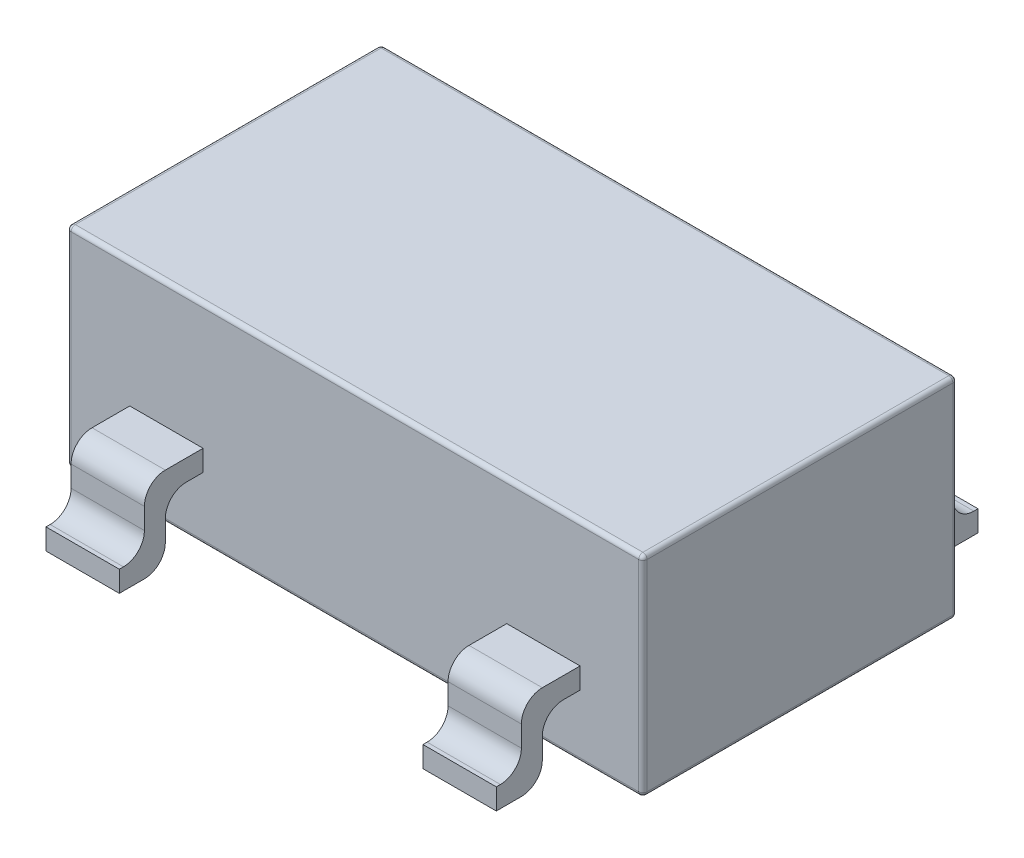
SolidWorks part; units mm, degrees
ref_plane "Front Plane" through (0, 0, 0) normal (0, 0, 1) x (1, 0, 0)
ref_plane "Top Plane" through (0, 0, 0) normal (0, 1, 0) x (1, 0, 0)
ref_plane "Right Plane" through (0, 0, 0) normal (1, 0, 0) x (0, 0, -1)
sketch "Sketch1" plane through (0, 0, 0) normal (0, 1, 0) x (1, 0, 0)
  line L1 (-1.375, -0.75) -> (1.375, -0.75)
  line L2 (-1.375, -0.75) -> (-1.375, 0.75)
  line L3 (-1.375, 0.75) -> (1.375, 0.75)
  line L4 (1.375, -0.75) -> (1.375, 0.75)
  line L5 (-1.375, -0.75) -> (1.375, 0.75) construction
  line L6 (-1.375, 0.75) -> (1.375, -0.75) construction
  point P0 (0, 0)
  dimension "D1" = 1.5
  dimension "D2" = 2.75
extrude "Boss-Extrude1" add sketch "Sketch1" along normal blind 1
sketch "Sketch2" plane through (0, 0, 0) normal (0, 1, 0) x (1, 0, 0)
  line L0 (-1.375, -0.75) -> (1.375, -0.75) construction
  line L1 (-1.075, -0.75) -> (-0.725, -0.75)
  line L2 (-1.075, -0.75) -> (-1.075, -1.15)
  line L3 (-1.075, -1.15) -> (-0.725, -1.15)
  line L4 (-0.725, -0.75) -> (-0.725, -1.15)
  line L5 (-1.075, -0.75) -> (-0.725, -1.15) construction
  line L6 (-1.075, -1.15) -> (-0.725, -0.75) construction
  line L12 (-1.375, 0) -> (1.375, 0) construction
  line L13 (1.375, -0.75) -> (1.375, 0.75) construction
  line L14 (0, -0.75) -> (0, 0.75) construction
  line L15 (1.375, 0.75) -> (-1.375, 0.75) construction
  line L16 (1.075, -1.15) -> (0.725, -0.75) construction
  line L17 (1.075, -0.75) -> (0.725, -1.15) construction
  line L18 (0.725, -0.75) -> (0.725, -1.15)
  line L19 (1.075, -1.15) -> (0.725, -1.15)
  line L20 (1.075, -0.75) -> (1.075, -1.15)
  line L21 (1.075, -0.75) -> (0.725, -0.75)
  line L22 (1.075, 0.75) -> (0.725, 1.15) construction
  line L23 (1.075, 1.15) -> (0.725, 0.75) construction
  line L24 (-1.075, 1.15) -> (-0.725, 0.75) construction
  line L25 (-1.075, 0.75) -> (-0.725, 1.15) construction
  line L26 (1.075, 0.75) -> (0.725, 0.75)
  line L27 (1.075, 0.75) -> (1.075, 1.15)
  line L28 (1.075, 1.15) -> (0.725, 1.15)
  line L29 (0.725, 0.75) -> (0.725, 1.15)
  line L30 (-0.725, 0.75) -> (-0.725, 1.15)
  line L31 (-1.075, 1.15) -> (-0.725, 1.15)
  line L32 (-1.075, 0.75) -> (-1.075, 1.15)
  line L33 (-1.075, 0.75) -> (-0.725, 0.75)
  line L34 (-0.1631, 0.75) -> (0.1869, 0.75)
  line L35 (0.1869, 0.75) -> (0.1869, 1.15)
  line L36 (0.1869, 1.15) -> (-0.1631, 1.15)
  line L37 (-0.1631, 1.15) -> (-0.1631, 0.75)
  point P4 (-0.9, -0.95)
  point P13 (0, 0)
  point P18 (0, 0)
  point P22 (0.9, -0.95)
  point P31 (0.9, 0.95)
  point P32 (-0.9, 0.95)
  point P36 (0.0119, 0.75)
  dimension "D1" = 0.9
  dimension "D2" = 0.4
  dimension "D3" = 0.35
  dimension "D4" = 0.35
extrude "Boss-Extrude2" add sketch "Sketch2" along normal blind 0.4
sketch "Sketch3" plane through (1.075, 0, 0) normal (1, 0, 0) x (0, 0, -1)
  line L0 (1.0302, 0) -> (1.15, 0)
  line L1 (1.15, 0) -> (1.15, 0.1)
  line L2 (1.0302, 0.3) -> (1.0302, 0.2)
  line L3 (0.75, 0.4) -> (0.9302, 0.4)
  line L4 (0.75, 0.3) -> (0.8302, 0.3)
  line L5 (0.75, 0.4) -> (1.15, 0.4) construction
  line L6 (0.75, 0.3) -> (0.9302, 0.3) construction
  line L7 (0.9302, 0.3) -> (0.9302, 0.054) construction
  line L8 (1.0302, 0.4) -> (1.0302, 0.054) construction
  line L9 (0.75, 0.4) -> (1.0302, 0.4) construction
  line L10 (0.9302, 0.2) -> (0.9302, 0.1)
  line L11 (1.15, 0.4) -> (1.15, 0) construction
  line L12 (0.75, 0) -> (1.15, 0) construction
  line L13 (1.15, 0.1) -> (1.1302, 0.1)
  line L14 (0, 0) -> (0, 1.2667) construction
  line L15 (-0.75, 0) -> (0.75, 0) construction
  line L16 (-1.15, 0.1) -> (-1.1302, 0.1)
  line L17 (-0.9302, 0.2) -> (-0.9302, 0.1)
  line L18 (-0.75, 0.3) -> (-0.8302, 0.3)
  line L19 (-0.75, 0.4) -> (-0.9302, 0.4)
  line L20 (-1.0302, 0.3) -> (-1.0302, 0.2)
  line L21 (-1.15, 0) -> (-1.15, 0.1)
  line L22 (-1.0302, 0) -> (-1.15, 0)
  line L23 (1.5636, 0.7221) -> (0.75, 0.7221)
  line L24 (-1.4393, 0.7221) -> (-1.4393, -0.2628)
  line L25 (-1.4393, -0.2628) -> (1.5636, -0.2628)
  line L26 (1.5636, -0.2628) -> (1.5636, 0.7221)
  line L27 (-0.75, 0) -> (-0.75, 0.7221)
  line L28 (-0.75, 1) -> (-0.75, 0) construction
  line L29 (-0.75, 0) -> (0.75, 0)
  line L30 (0.75, 0) -> (0.75, 0.7221)
  line L31 (0.75, 1) -> (0.75, 0) construction
  line L32 (-0.75, 0.7221) -> (-1.4393, 0.7221)
  arc A0 (0.8302, 0.3) -> (0.9302, 0.2) centre (0.8302, 0.2) cw
  arc A1 (1.0302, 0.3) -> (0.9302, 0.4) centre (0.9302, 0.3) ccw
  arc A2 (0.9302, 0.1) -> (1.0302, 0) centre (1.0302, 0.1) ccw
  arc A3 (1.0302, 0.2) -> (1.1302, 0.1) centre (1.1302, 0.2) ccw
  arc A4 (-1.0302, 0.2) -> (-1.1302, 0.1) centre (-1.1302, 0.2) cw
  arc A5 (-0.9302, 0.1) -> (-1.0302, 0) centre (-1.0302, 0.1) cw
  arc A6 (-1.0302, 0.3) -> (-0.9302, 0.4) centre (-0.9302, 0.3) cw
  arc A7 (-0.8302, 0.3) -> (-0.9302, 0.2) centre (-0.8302, 0.2) ccw
  point P29 (0.9302, 0)
  point P50 (-0.9302, 0)
  line M8 (0.75, 0) -> (1.15, 0)
  line M9 (1.15, 0) -> (1.15, 0.4)
  line M10 (1.15, 0.4) -> (0.75, 0.4)
  line M11 (0.75, 0.4) -> (0.75, 0)
  dimension "D2" = 0.1
  dimension "D3" = 0.1
  dimension "D4" = 0.1
  dimension "D5" = 0.1
  dimension "D1" = 0.1
extrude "Cut-Extrude1" cut sketch "Sketch3" against normal through all contours L18 A7 L17 A5 L22 L21 L16 A4 L20 A6 L19 L27 L32 L24 L25 L26 L23 L30 L29 M10 M9 M8 | A2 L10 A0 L4 M11 M8 | L2 A3 L13 A1 M9 M10
fillet "Fillet1" radius 0.02 12 edges at (0, 1, -0.75) (-1.375, 1, 0) (-1.375, 0.5, 0.75) (-1.375, 0.5, -0.75) (-1.375, 0, 0) (0, 0, -0.75) (1.375, 0.5, -0.75) (1.375, 0, 0) (1.375, 1, 0) (0, 0, 0.75) (0, 1, 0.75) (1.375, 0.5, 0.75)
